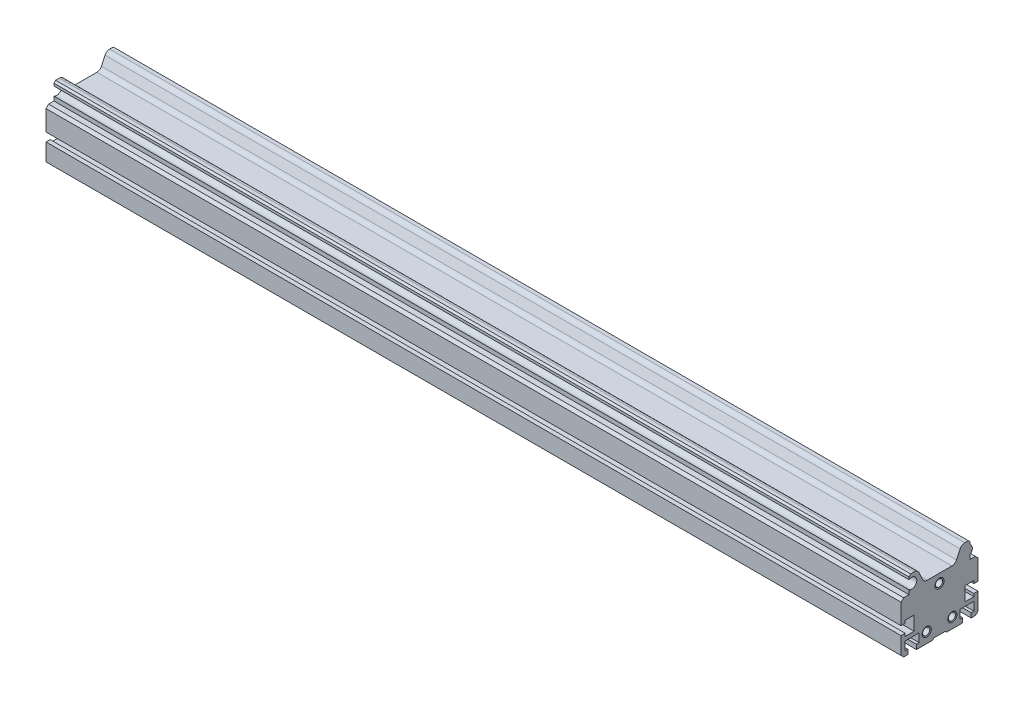
SolidWorks part; units mm, degrees
ref_plane "Front Plane" through (0, 0, 0) normal (0, 0, 1) x (1, 0, 0)
ref_plane "Top Plane" through (0, 0, 0) normal (0, 1, 0) x (1, 0, 0)
ref_plane "Right Plane" through (0, 0, 0) normal (1, 0, 0) x (0, 0, -1)
ref_plane "평면1" through (400, 0, 0) normal (1, 0, 0) x (0, 0, -1)
sketch "스케치1" plane through (400, 0, 0) normal (1, 0, 0) x (0, 0, -1)
  line L0 (-17.85, 38.2) -> (-17.85, -0.8)
  line L1 (-17.85, -0.8) -> (22.5, -0.8)
  line L2 (22.5, -0.8) -> (22.5, 39.2)
  line L3 (22.5, 39.2) -> (-16.85, 39.2)
  line L4 (-16.85, 39.2) -> (-17.85, 38.2)
extrude "보스-돌출1" add sketch "스케치1" against normal blind 500
sketch "스케치2" plane through (0, 0, 17.85) normal (0, 0, 1) x (1, 0, 0)
  line L0 (400, 29.2) -> (400, -0.8)
  line L1 (400, -0.8) -> (-100, -0.8)
  line L2 (-100, -0.8) -> (-100, 29.2)
  line L3 (-100, 29.2) -> (400, 29.2)
  line L4 (400, 38.2) -> (400, -0.8) construction
  dimension "D1" = 500
extrude "보스-돌출2" add sketch "스케치2" along normal blind 4.65
sketch "스케치3" plane through (-100, 0, 0) normal (-1, 0, 0) x (0, 0, 1)
  line L0 (22.5, 10.8) -> (22.5, 15.8)
  line L1 (22.5, 15.8) -> (20.1, 15.8)
  line L2 (20.1, 15.8) -> (20.1, 17.4)
  line L3 (20.1, 17.4) -> (14.9, 17.4)
  line L4 (14.9, 17.4) -> (14.9, 9.2)
  line L5 (14.9, 9.2) -> (20.1, 9.2)
  line L6 (20.1, 9.2) -> (20.1, 10.8)
  line L7 (20.1, 10.8) -> (22.5, 10.8)
extrude "컷-돌출1" cut sketch "스케치3" against normal through all
sketch "스케치4" plane through (-100, 0, 0) normal (-1, 0, 0) x (0, 0, 1)
  line L0 (13.5, -0.8) -> (18.5, -0.8)
  line L1 (18.5, -0.8) -> (18.5, 1.9)
  line L2 (18.5, 1.9) -> (20.1, 1.9)
  line L3 (20.1, 1.9) -> (20.1, 6.9)
  line L4 (20.1, 6.9) -> (11.9, 6.9)
  line L5 (11.9, 6.9) -> (11.9, 1.9)
  line L6 (11.9, 1.9) -> (13.5, 1.9)
  line L7 (13.5, 1.9) -> (13.5, -0.8)
extrude "컷-돌출2" cut sketch "스케치4" against normal through all
sketch "스케치5" plane through (-100, 0, 0) normal (-1, 0, 0) x (0, 0, 1)
  line L0 (-3.35, -0.8) -> (3.35, -0.8)
  line L1 (3.35, -0.8) -> (3.35, 0)
  line L2 (3.35, 0) -> (-3.35, 0)
  line L3 (-3.35, 0) -> (-3.35, -0.8)
extrude "컷-돌출3" cut sketch "스케치5" against normal through all
sketch "스케치6" plane through (-100, 0, 0) normal (-1, 0, 0) x (0, 0, 1)
  line L0 (-18.5, -0.8) -> (-13.5, -0.8)
  line L1 (-13.5, -0.8) -> (-13.5, 1.9)
  line L2 (-13.5, 1.9) -> (-11.9, 1.9)
  line L3 (-11.9, 1.9) -> (-11.9, 6.9)
  line L4 (-11.9, 6.9) -> (-20.1, 6.9)
  line L5 (-20.1, 6.9) -> (-20.1, 1.9)
  line L6 (-20.1, 1.9) -> (-18.5, 1.9)
  line L7 (-18.5, 1.9) -> (-18.5, -0.8)
extrude "컷-돌출4" cut sketch "스케치6" against normal through all
sketch "스케치7" plane through (-100, 0, 0) normal (-1, 0, 0) x (0, 0, 1)
  line L0 (-22.5, 15.8) -> (-22.5, 10.8)
  line L1 (-22.5, 10.8) -> (-20.1, 10.8)
  line L2 (-20.1, 10.8) -> (-20.1, 9.2)
  line L3 (-20.1, 9.2) -> (-14.9, 9.2)
  line L4 (-14.9, 9.2) -> (-14.9, 17.4)
  line L5 (-14.9, 17.4) -> (-20.1, 17.4)
  line L6 (-20.1, 17.4) -> (-20.1, 15.8)
  line L7 (-20.1, 15.8) -> (-22.5, 15.8)
extrude "컷-돌출5" cut sketch "스케치7" against normal through all
sketch "스케치8" plane through (-100, 0, 0) normal (-1, 0, 0) x (0, 0, 1)
  line L0 (-17.85, 36.7055) -> (-17.85, 39.2)
  line L1 (-17.85, 39.2) -> (-22.5, 39.2)
  line L2 (-22.5, 39.2) -> (-22.5, 29.2)
  line L3 (-22.5, 29.2) -> (-17.85, 29.2)
  line L4 (-17.85, 29.2) -> (-17.85, 31.6945)
  arc A0 (-17.85, 31.6945) -> (-17.85, 36.7055) centre (-16.2, 34.2) cw
extrude "컷-돌출6" cut sketch "스케치8" against normal through all
sketch "스케치9" plane through (-100, 0, 0) normal (-1, 0, 0) x (0, 0, 1)
  line L0 (-9.1195, 39.2) -> (-9.1195, 31.2)
  line L1 (-9.1195, 31.2) -> (9.1195, 31.2)
  line L2 (9.1195, 31.2) -> (9.1195, 39.2)
  line L3 (9.1195, 39.2) -> (-9.1195, 39.2)
extrude "컷-돌출7" cut sketch "스케치9" against normal through all
draft "구배1" type of draft neutral plane draft angle 45 faces to draft 2 face at (150, -0.4, 3.35) face at (150, -0.4, -3.35) neutral plane through (400, 0, 3.35) neutral plane normal (0, -1, 0) parameters "D1"=45
draft "구배2" type of draft neutral plane draft angle 24.775 faces to draft 2 face at (150, 35.2, 9.1195) face at (150, 35.2, -9.1195) neutral plane through (400, 31.2, -9.1195) neutral plane normal (0, 1, 0) parameters "D1"=24.775
hole_wizard "Ø4.2 (4.2) Diameter Hole1" positions "스케치11" profile "스케치10" hole size "Ø4.2" standard "ANSI Metric"
sketch "스케치11" plane through (400, 0, 0) normal (1, 0, 0) x (0, 0, -1)
  point P0 (-7.5, 5.25)
  point P1 (7.5, 5.25)
  point P2 (0, 26)
sketch "스케치10" plane through (400, 5.25, 7.5) normal (0, 1, 0) x (0, 0, -1)
  line L0 (0, 0) -> (0, 500)
  line L1 (0, 500) -> (2.1, 500)
  line L2 (2.1, 500) -> (2.1, 0)
  line L5 (2.1, 0) -> (0, 0)
  line L11 (0, -6.35) -> (0, 107.95) construction
  dimension "Thru Hole Dia." = 4.2
  dimension "Thru Hole Depth" = 500
hole_wizard "Ø6.0 (6) Diameter Hole1" positions "스케치13" profile "스케치12" hole size "Ø6.0" standard "ANSI Metric"
sketch "스케치13" plane through (-100, 0, 0) normal (-1, 0, 0) x (0, 0, 1)
  point P0 (16.2907, 34.2)
sketch "스케치12" plane through (-100, 34.2, 16.2907) normal (0, 1, 0) x (0, 0, 1)
  line L0 (0, 0) -> (0, 500)
  line L1 (0, 500) -> (3, 500)
  line L2 (3, 500) -> (3, 0)
  line L5 (3, 0) -> (0, 0)
  line L11 (0, -6.35) -> (0, 107.95) construction
  dimension "Thru Hole Dia." = 6
  dimension "Thru Hole Depth" = 500
chamfer "모따기1" distance 0.6 angle 25 3 edges at (400, 5.25, -9.6) (400, 5.25, 5.4) (400, 26, -2.1)
chamfer "모따기2" distance 0.6 angle 45 3 edges at (-100, 5.25, -9.6) (-100, 26, -2.1) (-100, 5.25, 5.4)
chamfer "모따기3" distance 1 angle 45 1 edges at (150, 39.2, -17.85)
chamfer "모따기4" distance 1.5 angle 45 4 edges at (150, -0.8, -22.5) (150, 29.2, 22.5) (150, 29.2, -22.5) (150, -0.8, 22.5)
fillet "필렛1" radius 3 4 edges at (150, 31.2, -9.1195) (150, 31.2, 9.1195) (150, 39.2, -12.8118) (150, 39.2, 12.8118)
